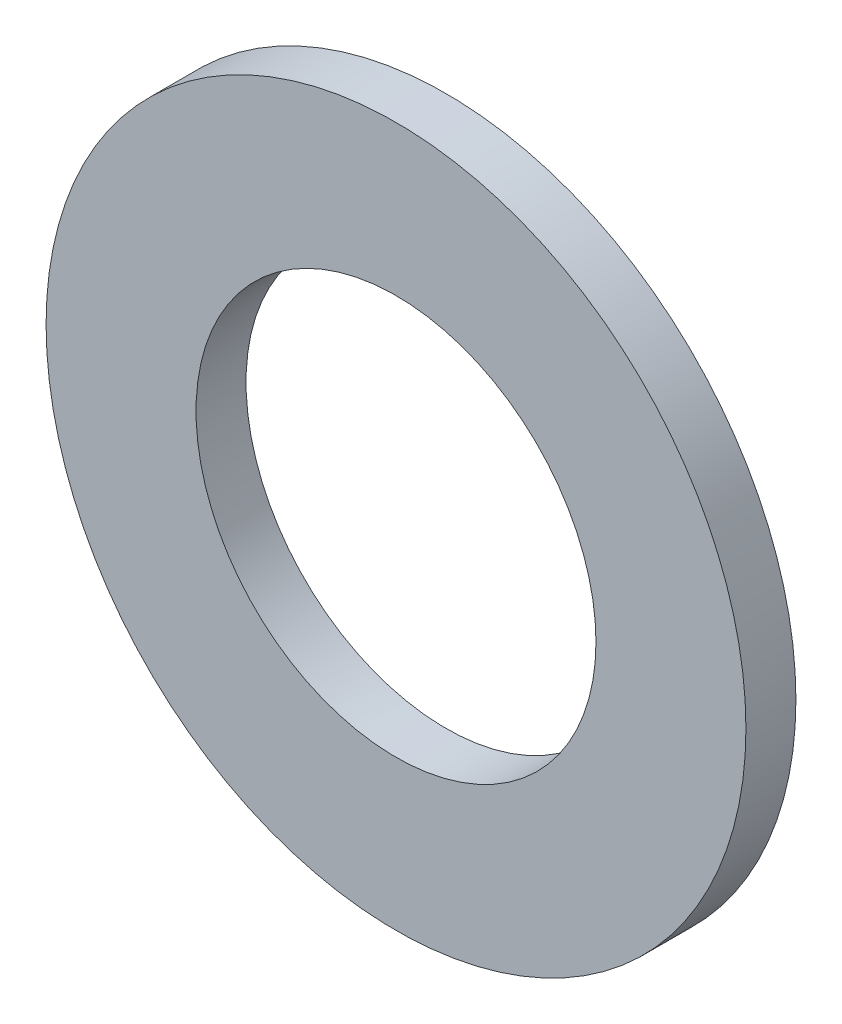
SolidWorks part; units mm, degrees
ref_plane "Front Plane" through (0, 0, 0) normal (0, 0, 1) x (1, 0, 0)
ref_plane "Top Plane" through (0, 0, 0) normal (0, 1, 0) x (1, 0, 0)
ref_plane "Right Plane" through (0, 0, 0) normal (1, 0, 0) x (0, 0, -1)
sketch "Sketch1" plane through (0, 0, 0) normal (0, 0, 1) x (1, 0, 0)
  circle A0 centre (0, 0) radius 7
  circle A1 centre (0, 0) radius 4
  dimension "D1" = 14
  dimension "D2" = 8
extrude "Boss-Extrude1" add sketch "Sketch1" along normal blind 1
